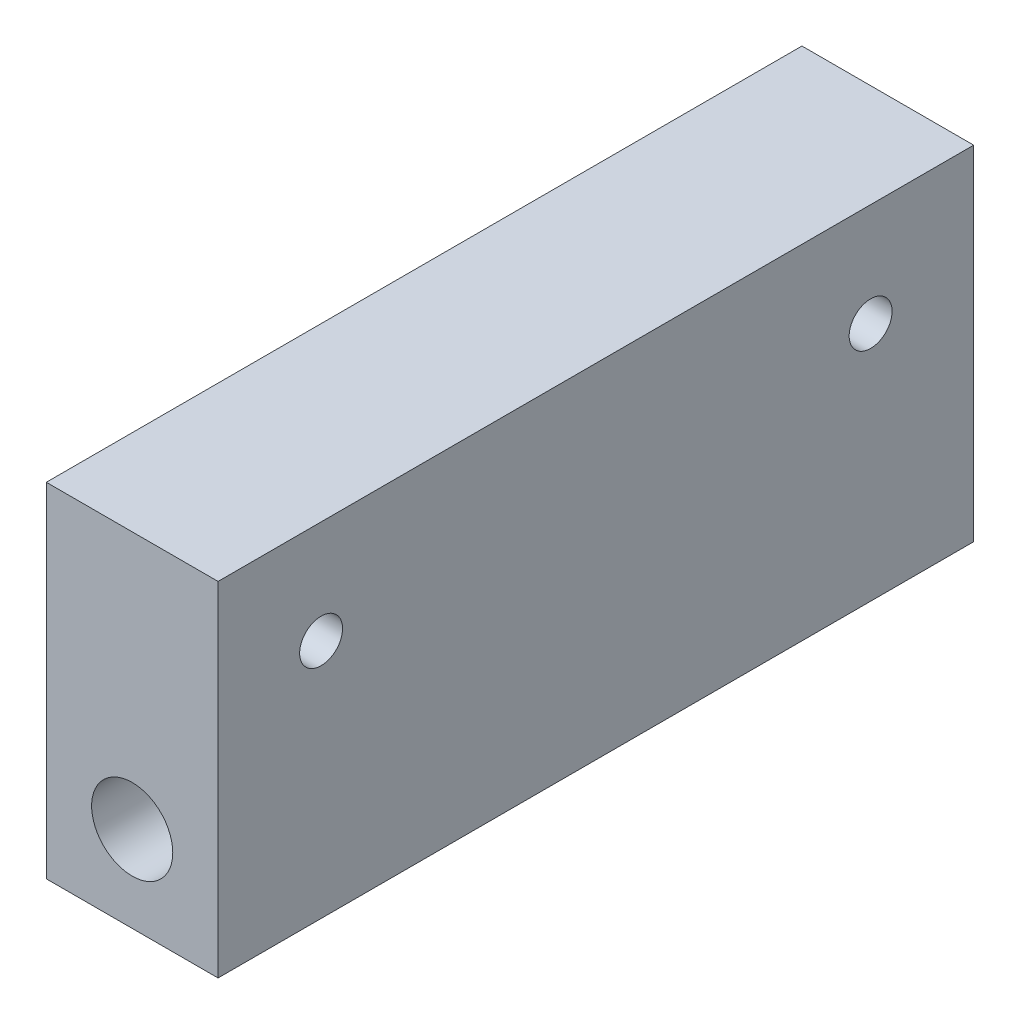
SolidWorks part; units mm, degrees
ref_plane "Front Plane" through (0, 0, 0) normal (0, 0, 1) x (1, 0, 0)
ref_plane "Top Plane" through (0, 0, 0) normal (0, 1, 0) x (1, 0, 0)
ref_plane "Right Plane" through (0, 0, 0) normal (1, 0, 0) x (0, 0, -1)
sketch "Sketch1" plane through (0, 0, 0) normal (0, 0, 1) x (1, 0, 0)
  line L1 (0, 0) -> (31.75, 0)
  line L2 (0, 0) -> (0, 63.5)
  line L3 (0, 63.5) -> (31.75, 63.5)
  line L4 (31.75, 0) -> (31.75, 63.5)
  circle A0 centre (15.875, 15.875) radius 7.5
  dimension "D1" = 63.5
  dimension "D2" = 31.75
extrude "Boss-Extrude1" add sketch "Sketch1" against normal blind 139.7
sketch "Sketch2" plane through (31.75, 0, 0) normal (1, 0, 0) x (0, 0, -1)
  line L0 (19.05, 44.45) -> (120.65, 44.45)
  line L1 (0, 0) -> (0, 63.5) construction
  line L2 (139.7, 0) -> (139.7, 63.5) construction
  line L3 (139.7, 63.5) -> (0, 63.5) construction
  circle A0 centre (19.05, 44.45) radius 3.9687
  circle A1 centre (120.65, 44.45) radius 3.9687
  dimension "D1" = 7.9375
  dimension "D2" = 7.9375
  dimension "D3" = 19.05
  dimension "D4" = 19.05
  dimension "D5" = 19.05
extrude "Cut-Extrude1" cut sketch "Sketch2" against normal blind 139.7
